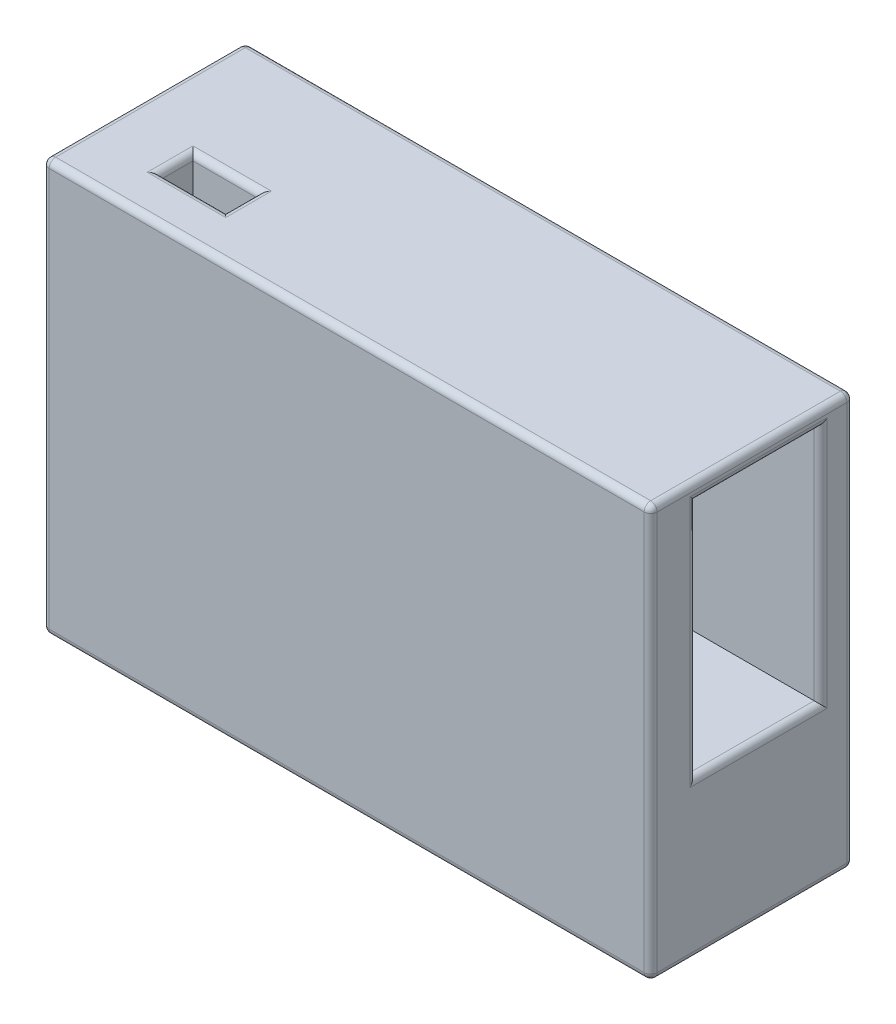
SolidWorks part; units mm, degrees
ref_plane "Front Plane" through (0, 0, 0) normal (0, 0, 1) x (1, 0, 0)
ref_plane "Top Plane" through (0, 0, 0) normal (0, 1, 0) x (1, 0, 0)
ref_plane "Right Plane" through (0, 0, 0) normal (1, 0, 0) x (0, 0, -1)
sketch "Sketch1" plane through (0, 0, 0) normal (0, 0, 1) x (1, 0, 0)
  line L5 (-46.5, -31.5) -> (46.5, -31.5)
  line L6 (-46.5, -31.5) -> (-46.5, 31.5)
  line L7 (-46.5, 31.5) -> (46.5, 31.5)
  line L8 (46.5, -31.5) -> (46.5, 31.5)
  line L9 (-46.5, -31.5) -> (46.5, 31.5) construction
  line L10 (-46.5, 31.5) -> (46.5, -31.5) construction
  point P0 (0, 0)
extrude "Boss-Extrude1" add sketch "Sketch1" along normal blind 31
sketch "Sketch2" plane through (46.5, 0, 0) normal (1, 0, 0) x (0, 0, -1)
  line L0 (-31, -31.5) -> (-31, 31.5) construction
  line L1 (-24, 29) -> (-5, 29)
  line L2 (-24, 29) -> (-24, -7.5)
  line L3 (-24, -7.5) -> (-5, -7.5)
  line L4 (-5, 29) -> (-5, -7.5)
  line L5 (0, -31.5) -> (0, 31.5) construction
  line L6 (-31, 31.5) -> (0, 31.5) construction
  line L7 (-31, -31.5) -> (0, -31.5) construction
  dimension "D1" = 7
  dimension "D2" = 5
  dimension "D3" = 2.5
  dimension "D4" = 24
extrude "Cut-Extrude1" cut sketch "Sketch2" against normal blind 31
sketch "Sketch3" plane through (0, 31.5, 0) normal (0, 1, 0) x (1, 0, 0)
  line L0 (46.5, -31) -> (-46.5, -31) construction
  line L1 (-35.5, -19) -> (-25.5, -19)
  line L2 (-35.5, -19) -> (-35.5, -24)
  line L3 (-35.5, -24) -> (-25.5, -24)
  line L4 (-25.5, -19) -> (-25.5, -24)
  line L5 (-46.5, -31) -> (-46.5, 0) construction
  dimension "D1" = 7
  dimension "D2" = 11
  dimension "D3" = 10
  dimension "D4" = 5
extrude "Cut-Extrude2" cut sketch "Sketch3" against normal blind 31
fillet "Fillet1" radius 1 20 edges at (-46.5, 0, 0) (-46.5, -31.5, 15.5) (0, -31.5, 0) (0, -31.5, 31) (-46.5, 0, 31) (46.5, -31.5, 15.5) (46.5, 0, 31) (46.5, 0, 0) (46.5, 10.75, 5) (46.5, 29, 14.5) (46.5, 10.75, 24) (46.5, -7.5, 14.5) (46.5, 31.5, 15.5) (0, 31.5, 31) (-46.5, 31.5, 15.5) (0, 31.5, 0) (-25.5, 31.5, 21.5) (-30.5, 31.5, 19) (-35.5, 31.5, 21.5) (-30.5, 31.5, 24)
